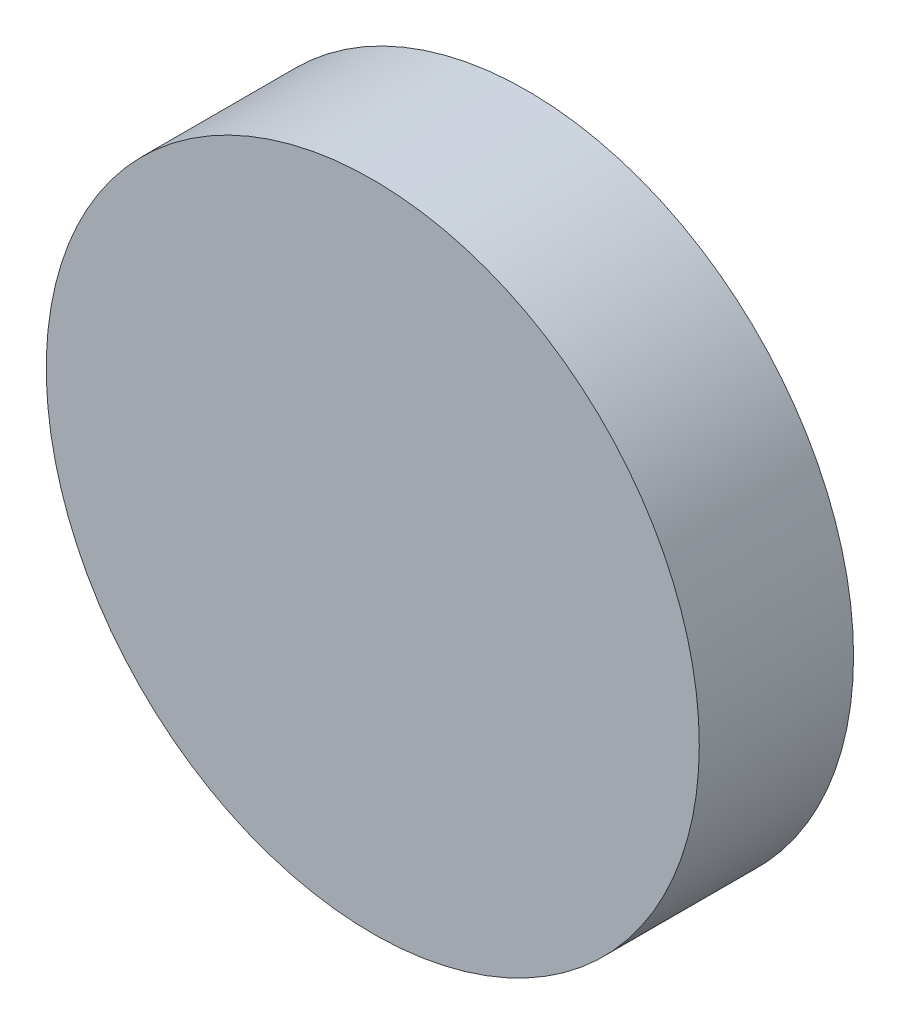
SolidWorks part; units mm, degrees
ref_plane "前视基准面" through (0, 0, 0) normal (0, 0, 1) x (1, 0, 0)
ref_plane "上视基准面" through (0, 0, 0) normal (0, 1, 0) x (1, 0, 0)
ref_plane "右视基准面" through (0, 0, 0) normal (1, 0, 0) x (0, 0, -1)
sketch "草图1" plane through (0, 0, 0) normal (0, 0, 1) x (1, 0, 0)
  circle A0 centre (0, 0) radius 12.7
  dimension "D1" = 25.4
extrude "凸台-拉伸1" add sketch "草图1" along normal blind 6 contours A0
